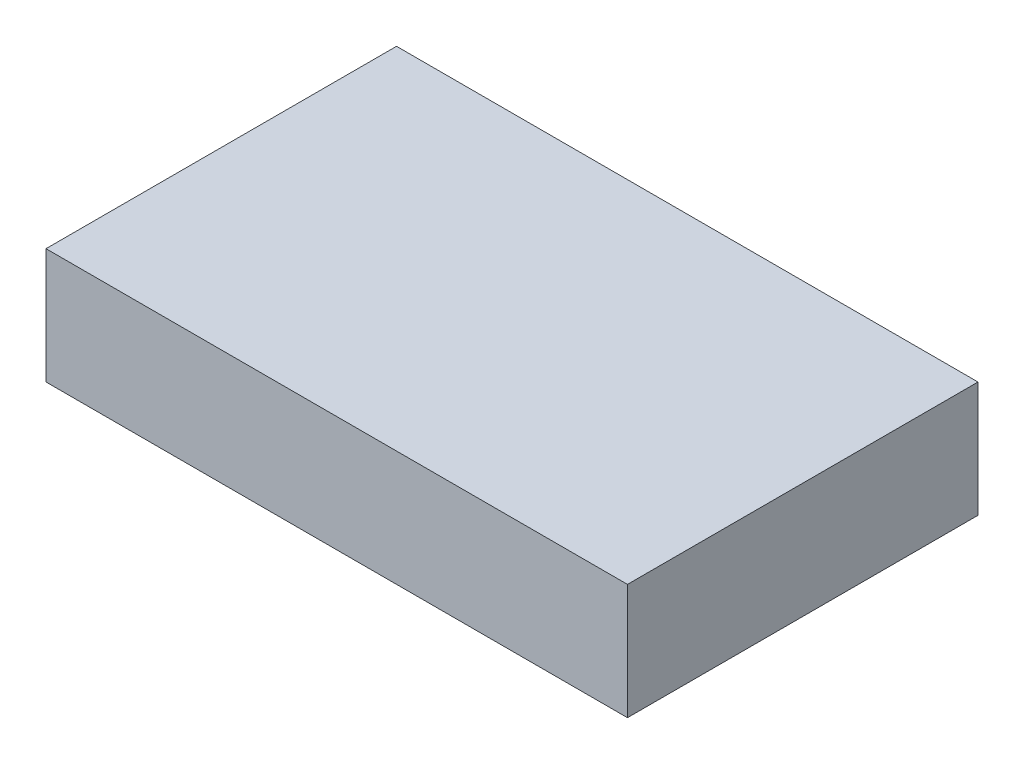
SolidWorks part; units mm, degrees
ref_plane "Front Plane" through (0, 0, 0) normal (0, 0, 1) x (1, 0, 0)
ref_plane "Top Plane" through (0, 0, 0) normal (0, 1, 0) x (1, 0, 0)
ref_plane "Right Plane" through (0, 0, 0) normal (1, 0, 0) x (0, 0, -1)
sketch "Sketch1" plane through (0, 0, 0) normal (0, 1, 0) x (1, 0, 0)
  line L1 (70.5, -42.5) -> (-70.5, -42.5)
  line L2 (70.5, -42.5) -> (70.5, 42.5)
  line L3 (70.5, 42.5) -> (-70.5, 42.5)
  line L4 (-70.5, -42.5) -> (-70.5, 42.5)
  line L5 (70.5, -42.5) -> (-70.5, 42.5) construction
  line L6 (70.5, 42.5) -> (-70.5, -42.5) construction
  point P0 (0, 0)
  dimension "D1" = 85
  dimension "D2" = 141
extrude "Boss-Extrude1" add sketch "Sketch1" along normal blind 28
